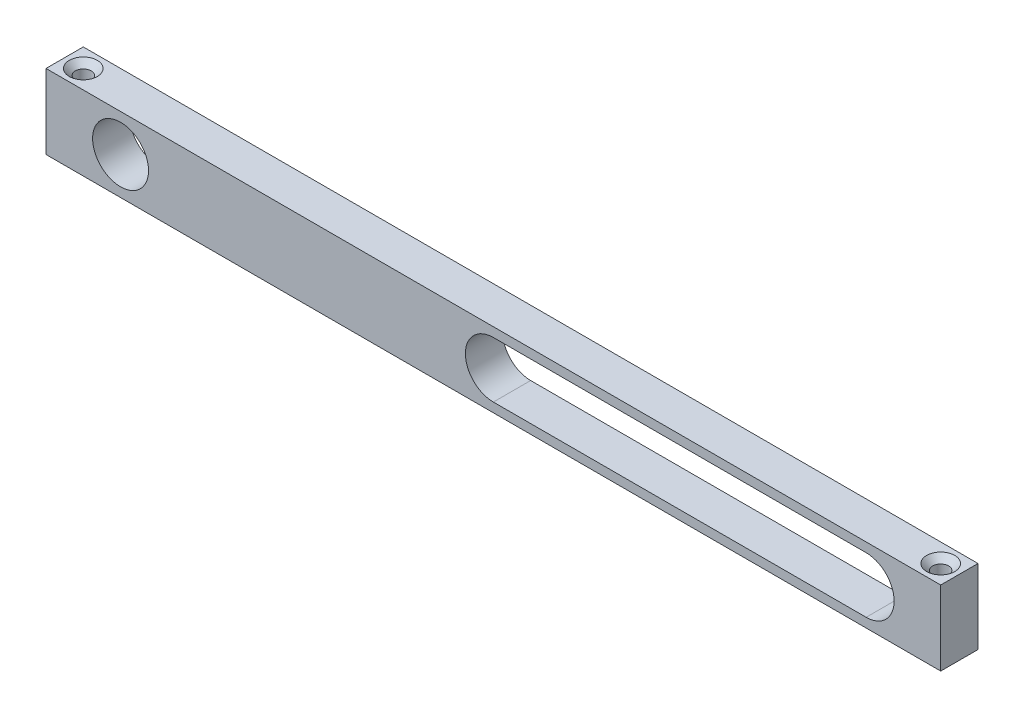
SolidWorks part; units mm, degrees
ref_plane "Front Plane" through (0, 0, 0) normal (0, 0, 1) x (1, 0, 0)
ref_plane "Top Plane" through (0, 0, 0) normal (0, 1, 0) x (1, 0, 0)
ref_plane "Right Plane" through (0, 0, 0) normal (1, 0, 0) x (0, 0, -1)
sketch "Sketch2" plane through (0, 0, 0) normal (0, 0, 1) x (1, 0, 0)
  line L1 (-76.2, -6.35) -> (76.2, -6.35)
  line L2 (-76.2, -6.35) -> (-76.2, 6.35)
  line L3 (-76.2, 6.35) -> (76.2, 6.35)
  line L4 (76.2, -6.35) -> (76.2, 6.35)
  line L5 (-76.2, -6.35) -> (76.2, 6.35) construction
  line L6 (-76.2, 6.35) -> (76.2, -6.35) construction
  line L7 (0, -4.7625) -> (63.5, -4.7625)
  line L9 (0, 4.7625) -> (63.5, 4.7625)
  arc A0 (63.5, -4.7625) -> (63.5, 4.7625) centre (63.5, 0) ccw
  arc A2 (0, 4.7625) -> (0, -4.7625) centre (0, 0) ccw
  circle A3 centre (-63.5, 0) radius 4.7625
  point P0 (0, 0)
  dimension "D3" = 9.525
  dimension "D6" = 9.525
  dimension "D1" = 152.4
  dimension "D2" = 12.7
  dimension "D4" = 6.35
  dimension "D5" = 63.5
  dimension "D7" = 63.5
  dimension "D8" = 6.35
extrude "Boss-Extrude1" add sketch "Sketch2" along normal blind 6.35
hole_wizard "#6-32 Tapped Hole1" positions "Sketch5" profile "Sketch4" tap size "#6-32" standard "ANSI Inch" end condition through all
sketch "Sketch5" plane through (0, 6.35, 0) normal (0, 1, 0) x (1, 0, 0)
  line L0 (76.2, 0) -> (-76.2, 0) construction
  line L1 (-76.2, -6.35) -> (-76.2, 0) construction
  point P0 (-73.025, -3.175)
  dimension "D1" = 3.175
  dimension "D2" = 3.175
sketch "Sketch4" plane through (-73.025, 6.35, 3.175) normal (1, 0, 0) x (0, 0, 1)
  line L0 (0, 0) -> (0, 12.7)
  line L1 (0, 12.7) -> (1.3525, 12.7)
  line L2 (1.3525, 12.7) -> (1.3525, 1.0351)
  line L3 (1.3525, 1.0351) -> (2.3876, 0)
  line L5 (2.3876, 0) -> (0, 0)
  line L6 (-1.3525, 1.0351) -> (-2.3876, 0) construction
  line L11 (0, -6.35) -> (0, 107.95) construction
  dimension "Thru Tap Drill Dia." = 2.7051
  dimension "Thru Tap Drill Depth" = 12.7
  dimension "Near C'Sink Dia." = 4.7752
  dimension "Near C'Sink Angle" = 90
cosmetic thread "Hole Thread1" parameters "D2"=3.5052
hole_wizard "#6-32 Tapped Hole2" positions "Sketch6" profile "Sketch7" tap size "#6-32" standard "ANSI Inch" end condition through all
sketch "Sketch6" plane through (0, 6.35, 0) normal (0, 1, 0) x (1, 0, 0)
  line L0 (76.2, 0) -> (-76.2, 0) construction
  line L1 (76.2, -6.35) -> (76.2, 0) construction
  point P0 (73.025, -3.175)
  dimension "D1" = 3.175
  dimension "D2" = 3.175
sketch "Sketch7" plane through (73.025, 6.35, 3.175) normal (1, 0, 0) x (0, 0, 1)
  line L0 (0, 0) -> (0, 12.7)
  line L1 (0, 12.7) -> (1.3525, 12.7)
  line L2 (1.3525, 12.7) -> (1.3525, 1.035)
  line L3 (1.3525, 1.035) -> (2.3876, 0)
  line L5 (2.3876, 0) -> (0, 0)
  line L6 (-1.3525, 1.035) -> (-2.3876, 0) construction
  line L11 (0, -6.35) -> (0, 107.95) construction
  dimension "Thru Tap Drill Dia." = 2.7051
  dimension "Thru Tap Drill Depth" = 12.7
  dimension "Near C'Sink Dia." = 4.7752
  dimension "Near C'Sink Angle" = 90
cosmetic thread "Hole Thread2"
